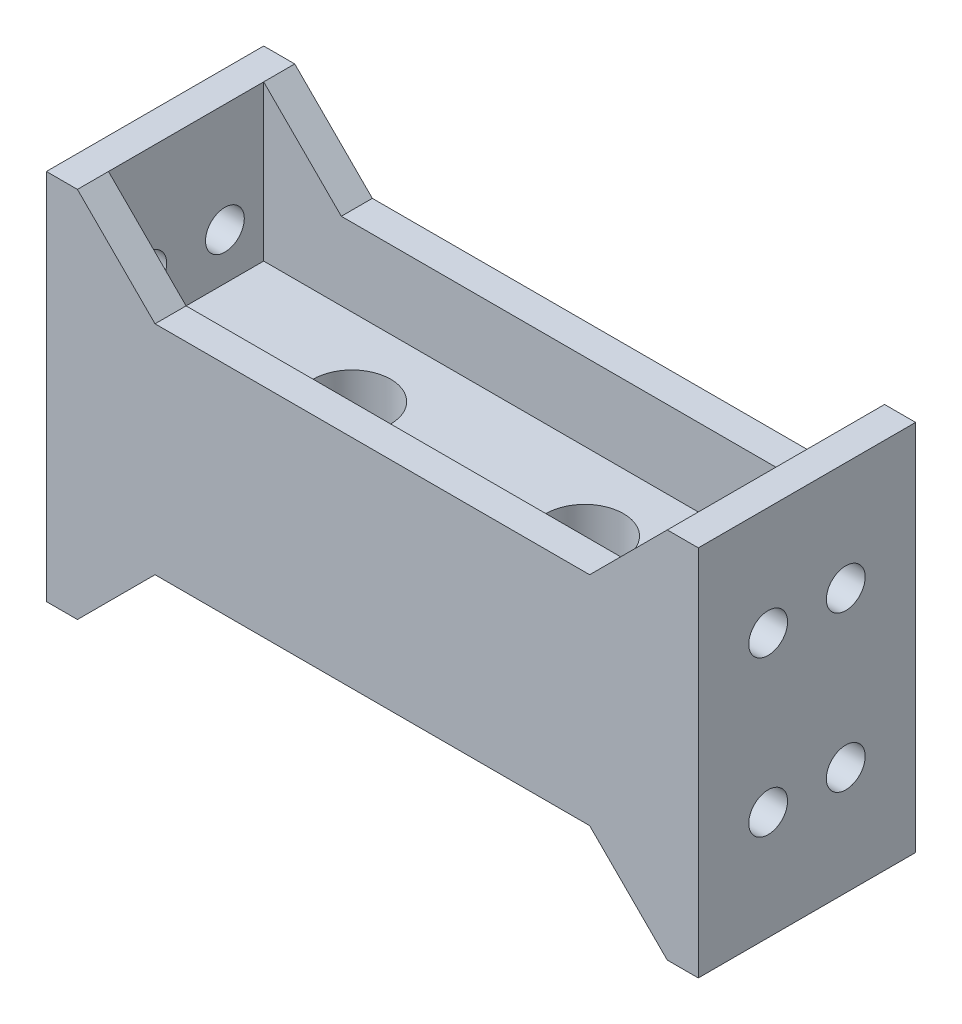
SolidWorks part; units mm, degrees
ref_plane "Front Plane" through (0, 0, 0) normal (0, 0, 1) x (1, 0, 0)
ref_plane "Top Plane" through (0, 0, 0) normal (0, 1, 0) x (1, 0, 0)
ref_plane "Right Plane" through (0, 0, 0) normal (1, 0, 0) x (0, 0, -1)
sketch "Sketch2" plane through (0, 0, 0) normal (0, 1, 0) x (1, 0, 0)
  line L1 (-21, 7) -> (21, 7)
  line L2 (-21, 7) -> (-21, -7)
  line L3 (-21, -7) -> (21, -7)
  line L4 (21, 7) -> (21, -7)
  line L5 (-21, 7) -> (21, -7) construction
  line L6 (-21, -7) -> (21, 7) construction
  point P0 (0, 0)
  dimension "D1" = 14
  dimension "D2" = 42
extrude "Boss-Extrude1" add sketch "Sketch2" along normal blind 4
sketch "Sketch3" plane through (0, 0, 0) normal (0, -1, 0) x (1, 0, 0)
  line L0 (21, -7) -> (-21, -7) construction
  line L1 (-21, 7) -> (-19, 7)
  line L2 (-21, 7) -> (-21, -7)
  line L3 (-21, -7) -> (-19, -7)
  line L4 (-19, 7) -> (-19, -7)
  line L5 (-21, 7) -> (21, 7) construction
  line L6 (21, 7) -> (19, 7)
  line L7 (21, 7) -> (21, -7)
  line L8 (21, -7) -> (19, -7)
  line L9 (19, 7) -> (19, -7)
  line L10 (21, 7) -> (21, -7) construction
  dimension "D1" = 2
  dimension "D2" = 2
extrude "Boss-Extrude2" add sketch "Sketch3" along normal blind 10
sketch "Sketch4" plane through (0, 0, 7) normal (0, 0, 1) x (1, 0, 0)
  line L5 (0, 4) -> (0, 0) construction
  line L6 (-21, 4) -> (21, 4) construction
  line L10 (-14, -5) -> (14, -5)
  line L13 (-19, -10) -> (-14, -5)
  line L14 (19, -10) -> (14, -5)
  line L15 (-19, 0) -> (19, 0) construction
  line L16 (-19, 0) -> (19, 0)
  line L17 (-19, -10) -> (-19, 0) construction
  line L18 (-19, -10) -> (-19, 0)
  line L19 (19, -10) -> (19, 0) construction
  line L20 (19, -10) -> (19, 0)
extrude "Boss-Extrude3" add sketch "Sketch4" against normal blind 2
mirror "Mirror1" about plane through (0, 0, 0) normal (0, 0, 1) of "Boss-Extrude3"
sketch "Sketch5" plane through (0, 0, 0) normal (0, -1, 0) x (1, 0, 0)
  line L0 (-19, 0) -> (19, 0) construction
  line L1 (-19, -5) -> (-19, 5) construction
  line L2 (19, 5) -> (19, -5) construction
  circle A0 centre (-8.3199, 0) radius 2.5
  circle A1 centre (6.6801, 0) radius 2.5
  dimension "D1" = 5
  dimension "D2" = 5
  dimension "D3" = 15
extrude "Cut-Extrude1" cut sketch "Sketch5" against normal through all both and the other way through all
sketch "Sketch6" plane through (-19, 0, 0) normal (1, 0, 0) x (0, 0, -1)
  line L0 (5, -10) -> (-5, -10) construction
  line L1 (0, 0) -> (0, -10) construction
  line L2 (5, 0) -> (-5, 0) construction
  circle A0 centre (-2.5, -3) radius 1.25
  circle A1 centre (2.5, -3) radius 1.25
  dimension "D1" = 2.5
  dimension "D2" = 2.5
  dimension "D3" = 5
  dimension "D4" = 3
  dimension "D5" = 3
  dimension "D6" = 2.5
extrude "Cut-Extrude2" cut sketch "Sketch6" against normal blind 2
mirror "Mirror2" about plane through (0, 0, 0) normal (1, 0, 0) of "Cut-Extrude2"
sketch "Sketch7" plane through (0, 4, 0) normal (0, 1, 0) x (1, 0, 0)
  line L0 (-21, -7) -> (21, -7) construction
  line L1 (-21, 7) -> (-19, 7)
  line L2 (-21, 7) -> (-21, -7)
  line L3 (-21, -7) -> (-19, -7)
  line L4 (-19, 7) -> (-19, -7)
  line L6 (21, 7) -> (19, 7)
  line L7 (21, 7) -> (21, -7)
  line L8 (21, -7) -> (19, -7)
  line L9 (19, 7) -> (19, -7)
  dimension "D1" = 2
  dimension "D2" = 2
extrude "Boss-Extrude4" add sketch "Sketch7" along normal blind 10
sketch "Sketch8" plane through (-19, 0, 0) normal (1, 0, 0) x (0, 0, -1)
  line L0 (0, 14) -> (0, 4) construction
  line L1 (-7, 14) -> (7, 14) construction
  line L2 (-7, 4) -> (7, 4) construction
  line L3 (-7, 9) -> (7, 9) construction
  line L4 (-7, 14) -> (-7, 4) construction
  line L5 (7, 14) -> (7, 4) construction
  circle A0 centre (-2.5, 7) radius 1.25
  circle A1 centre (2.5, 7) radius 1.25
  dimension "D3" = 2.5
  dimension "D4" = 2.5
  dimension "D1" = 5
  dimension "D2" = 2.5
  dimension "D5" = 3
  dimension "D6" = 3
extrude "Cut-Extrude3" cut sketch "Sketch8" against normal blind 10
mirror "Mirror3" about plane through (0, 0, 0) normal (1, 0, 0) of "Cut-Extrude3"
sketch "Sketch9" plane through (0, 0, -7) normal (0, 0, -1) x (-1, 0, 0)
  line L2 (-19, 4) -> (19, 4) construction
  line L5 (0, 4) -> (0, 0) construction
  line L9 (19, 14) -> (19, 4) construction
  line L10 (-19, 14) -> (-19, 4) construction
  line L11 (19, 14) -> (19, 4)
  line L12 (-19, 4) -> (19, 4)
  line L13 (-19, 14) -> (-19, 4)
  line L14 (-14, 9) -> (14, 9)
  line L15 (-19, 14) -> (-14, 9)
  line L16 (19, 14) -> (14, 9)
extrude "Boss-Extrude5" add sketch "Sketch9" against normal blind 2
mirror "Mirror4" about plane through (0, 0, 0) normal (0, 0, 1) of "Boss-Extrude5"
